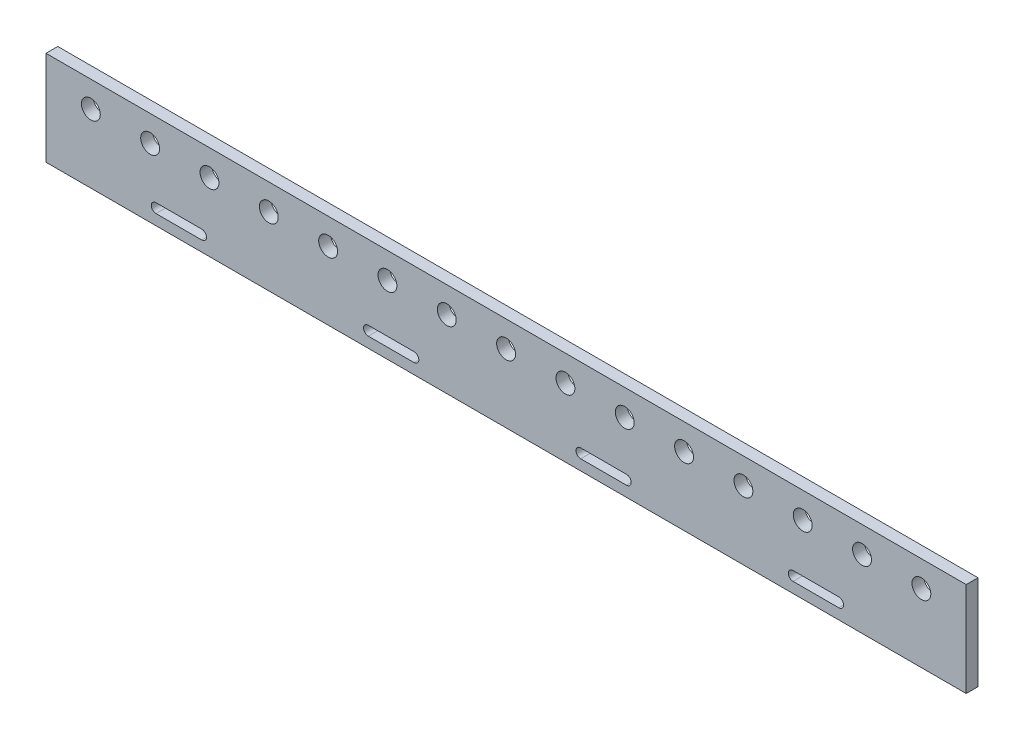
SolidWorks part; units mm, degrees
ref_plane "Ön Düzlem" through (0, 0, 0) normal (0, 0, 1) x (1, 0, 0)
ref_plane "Üst Düzlem" through (0, 0, 0) normal (0, 1, 0) x (1, 0, 0)
ref_plane "Sağ Düzlem" through (0, 0, 0) normal (1, 0, 0) x (0, 0, -1)
sketch "Çizim1" plane through (0, 0, 0) normal (0, 0, 1) x (1, 0, 0)
  line L1 (0, 0) -> (-390, 0)
  line L2 (0, 0) -> (0, -40)
  line L3 (0, -40) -> (-390, -40)
  line L4 (-390, 0) -> (-390, -40)
  circle A0 centre (-371, -11) radius 4
  circle A1 centre (-345.8571, -11) radius 4
  circle A2 centre (-320.7143, -11) radius 4
  circle A3 centre (-295.5714, -11) radius 4
  circle A4 centre (-270.4286, -11) radius 4
  circle A5 centre (-245.2857, -11) radius 4
  circle A6 centre (-220.1429, -11) radius 4
  circle A7 centre (-195, -11) radius 4
  circle A8 centre (-169.8571, -11) radius 4
  circle A9 centre (-144.7143, -11) radius 4
  circle A10 centre (-119.5714, -11) radius 4
  circle A11 centre (-94.4286, -11) radius 4
  circle A12 centre (-69.2857, -11) radius 4
  circle A13 centre (-44.1429, -11) radius 4
  circle A14 centre (-19, -11) radius 4
  dimension "D3" = 29
  dimension "D4" = 19
  dimension "D6" = 19
  dimension "D7" = 8
  dimension "D1" = 390
  dimension "D2" = 40
  dimension "D5" = 15
extrude "Yükseklik-Ekstrüzyon1" add sketch "Çizim1" along normal blind 5
sketch "Çizim2" plane through (0, 0, 5) normal (0, 0, 1) x (1, 0, 0)
  line L0 (-343.3954, -33.5279) -> (-323.9833, -33.5279) construction
  line L1 (-343.3954, -31.5279) -> (-323.9833, -31.5279)
  line L2 (-343.3954, -35.5279) -> (-323.9833, -35.5279)
  line L3 (-253.3954, -33.5279) -> (-233.9833, -33.5279) construction
  line L4 (-253.3954, -31.5279) -> (-233.9833, -31.5279)
  line L5 (-253.3954, -35.5279) -> (-233.9833, -35.5279)
  line L6 (-163.3954, -33.5279) -> (-143.9833, -33.5279) construction
  line L7 (-163.3954, -31.5279) -> (-143.9833, -31.5279)
  line L8 (-163.3954, -35.5279) -> (-143.9833, -35.5279)
  line L9 (-73.3954, -33.5279) -> (-53.9833, -33.5279) construction
  line L10 (-73.3954, -31.5279) -> (-53.9833, -31.5279)
  line L11 (-73.3954, -35.5279) -> (-53.9833, -35.5279)
  arc A0 (-343.3954, -31.5279) -> (-343.3954, -35.5279) centre (-343.3954, -33.5279) ccw
  arc A1 (-323.9833, -35.5279) -> (-323.9833, -31.5279) centre (-323.9833, -33.5279) ccw
  arc A2 (-253.3954, -31.5279) -> (-253.3954, -35.5279) centre (-253.3954, -33.5279) ccw
  arc A3 (-233.9833, -35.5279) -> (-233.9833, -31.5279) centre (-233.9833, -33.5279) ccw
  arc A4 (-163.3954, -31.5279) -> (-163.3954, -35.5279) centre (-163.3954, -33.5279) ccw
  arc A5 (-143.9833, -35.5279) -> (-143.9833, -31.5279) centre (-143.9833, -33.5279) ccw
  arc A6 (-73.3954, -31.5279) -> (-73.3954, -35.5279) centre (-73.3954, -33.5279) ccw
  arc A7 (-53.9833, -35.5279) -> (-53.9833, -31.5279) centre (-53.9833, -33.5279) ccw
  point P2 (-333.6893, -33.5279)
  point P11 (-243.6893, -33.5279)
  point P18 (-153.6893, -33.5279)
  point P25 (-63.6893, -33.5279)
  dimension "D1" = 4
  dimension "D2" = 4
extrude "Kes-Ekstrüzyon1" cut sketch "Çizim2" against normal blind 90
